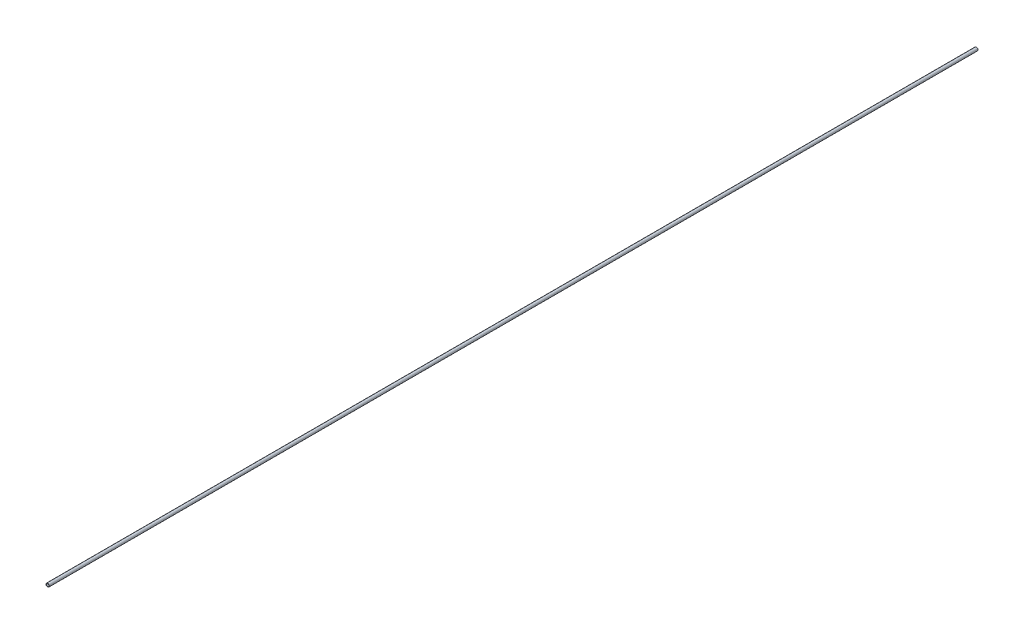
SolidWorks part; units mm, degrees
ref_plane "Front Plane" through (0, 0, 0) normal (0, 0, 1) x (1, 0, 0)
ref_plane "Top Plane" through (0, 0, 0) normal (0, 1, 0) x (1, 0, 0)
ref_plane "Right Plane" through (0, 0, 0) normal (1, 0, 0) x (0, 0, -1)
sketch "Sketch1" plane through (0, 0, 0) normal (0, 0, 1) x (1, 0, 0)
  circle A0 centre (0, 0) radius 10.668
  dimension "Pipe OD" = 21.336
extrude "Extrude-Thin1" add sketch "Sketch1" along normal mid plane 6000 thin thin type one direction reverse wall 2.7686
